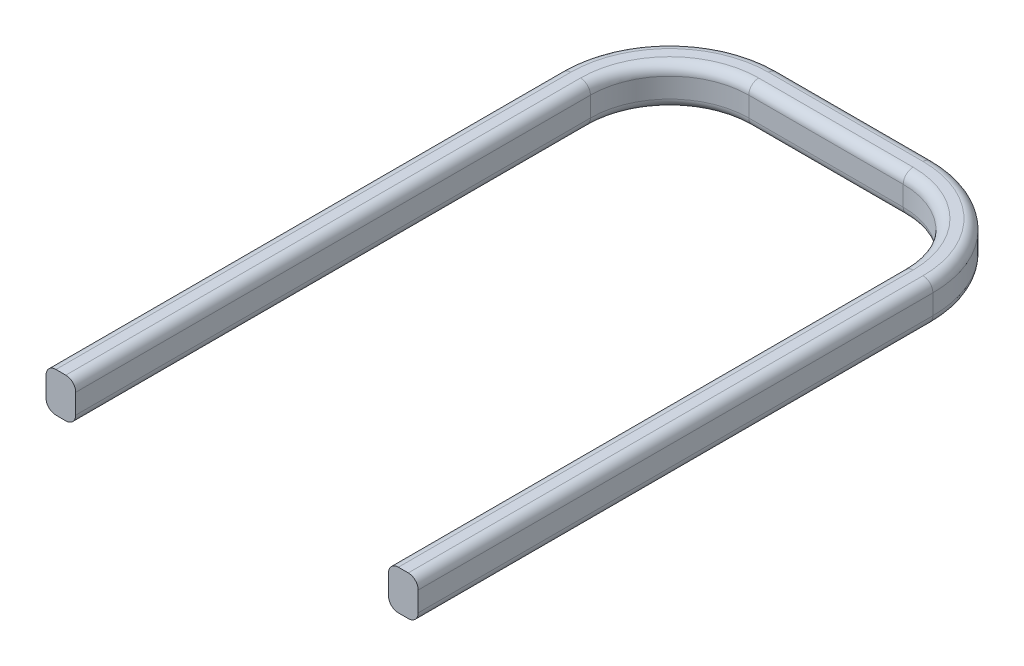
SolidWorks part; units mm, degrees
ref_plane "Front Plane" through (0, 0, 0) normal (0, 0, 1) x (1, 0, 0)
ref_plane "Top Plane" through (0, 0, 0) normal (0, 1, 0) x (1, 0, 0)
ref_plane "Right Plane" through (0, 0, 0) normal (1, 0, 0) x (0, 0, -1)
sketch "Sketch1" plane through (0, 0, 0) normal (0, 1, 0) x (1, 0, 0)
  line L0 (-4.7, 5.5) -> (-4.7, -7.5)
  line L1 (-1.95, 7.5) -> (1.95, 7.5)
  line L2 (-3.95, 5.5) -> (-3.95, -7.5)
  line L4 (3.95, 5.5) -> (3.95, -7.5)
  line L5 (-3.95, 7.5) -> (3.95, -7.5) construction
  line L6 (-3.95, -7.5) -> (3.95, 7.5) construction
  line L7 (-1.95, 8.25) -> (1.95, 8.25)
  line L8 (4.7, 5.5) -> (4.7, -7.5)
  line L9 (-4.7, -7.5) -> (-3.95, -7.5)
  line L10 (3.95, -7.5) -> (4.7, -7.5)
  arc A0 (1.95, 7.5) -> (3.95, 5.5) centre (1.95, 5.5) cw
  arc A1 (-3.95, 5.5) -> (-1.95, 7.5) centre (-1.95, 5.5) cw
  arc A2 (-4.7, 5.5) -> (-1.95, 8.25) centre (-1.95, 5.5) cw
  arc A3 (1.95, 8.25) -> (4.7, 5.5) centre (1.95, 5.5) cw
  point P0 (0, 0)
  dimension "D3" = 2
  dimension "D1" = 15
  dimension "D2" = 3.95
  dimension "D4" = 0.75
extrude "Boss-Extrude1" add sketch "Sketch1" along normal blind 1
fillet "Fillet1" radius 0.25 20 edges at (-4.7, 0, 1) (-3.8945, 0, -7.4445) (0, 0, -8.25) (3.8945, 0, -7.4445) (-3.95, 0, 1) (-3.3642, 0, -6.9142) (0, 0, -7.5) (3.3642, 0, -6.9142) (4.7, 1, 1) (3.8945, 1, -7.4445) (0, 1, -8.25) (-3.8945, 1, -7.4445) (3.95, 1, 1) (3.3642, 1, -6.9142) (0, 1, -7.5) (-3.3642, 1, -6.9142) (4.7, 0, 1) (3.95, 0, 1) (-4.7, 1, 1) (-3.95, 1, 1)
